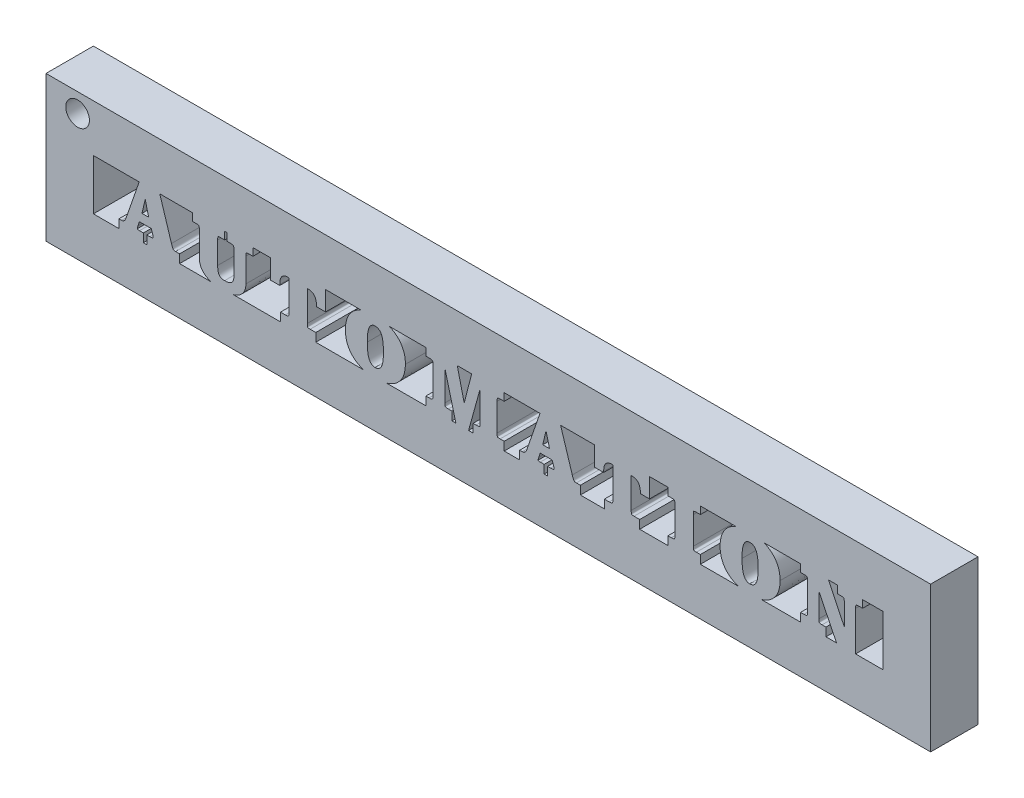
SolidWorks part; units mm, degrees
ref_plane "Front Plane" through (0, 0, 0) normal (0, 0, 1) x (1, 0, 0)
ref_plane "Top Plane" through (0, 0, 0) normal (0, 1, 0) x (1, 0, 0)
ref_plane "Right Plane" through (0, 0, 0) normal (1, 0, 0) x (0, 0, -1)
sketch "Sketch2" plane through (0, 0, 0) normal (0, 0, 1) x (1, 0, 0)
  line L0 (0, 0) -> (50, 0) construction
  text T0 "<b>AUTOMATION</b>" font "Clarendon Blk BT" height in points 12
  dimension "D1" = 50
extrude "Boss-Extrude1" add sketch "Sketch2" along normal blind 3
sketch "Sketch3" plane through (0, 0, 0) normal (0, 0, 1) x (1, 0, 0)
  line L0 (-3, -3) -> (-3, 6.2)
  line L1 (0, 0) -> (50, 0)
  line L2 (0, 0) -> (0, 3.2)
  line L3 (0, 3.2) -> (50, 3.2)
  line L4 (50, 0) -> (50, 3.2)
  line L5 (-3, 6.2) -> (53, 6.2)
  line L6 (53, -3) -> (53, 6.2)
  line L7 (-3, -3) -> (53, -3)
  point P9 (50, 0)
  dimension "D1" = 50
  dimension "D2" = 3.2
  dimension "D3" = 3
extrude "Boss-Extrude2" add sketch "Sketch3" along normal blind 3
sketch "Sketch4" plane through (0, 0, 3) normal (0, 0, 1) x (1, 0, 0)
  circle A0 centre (-1, 5) radius 0.75
  dimension "D2" = 1.5
  dimension "D1" = 2
  dimension "D3" = 8
extrude "Cut-Extrude1" cut sketch "Sketch4" against normal blind 3
